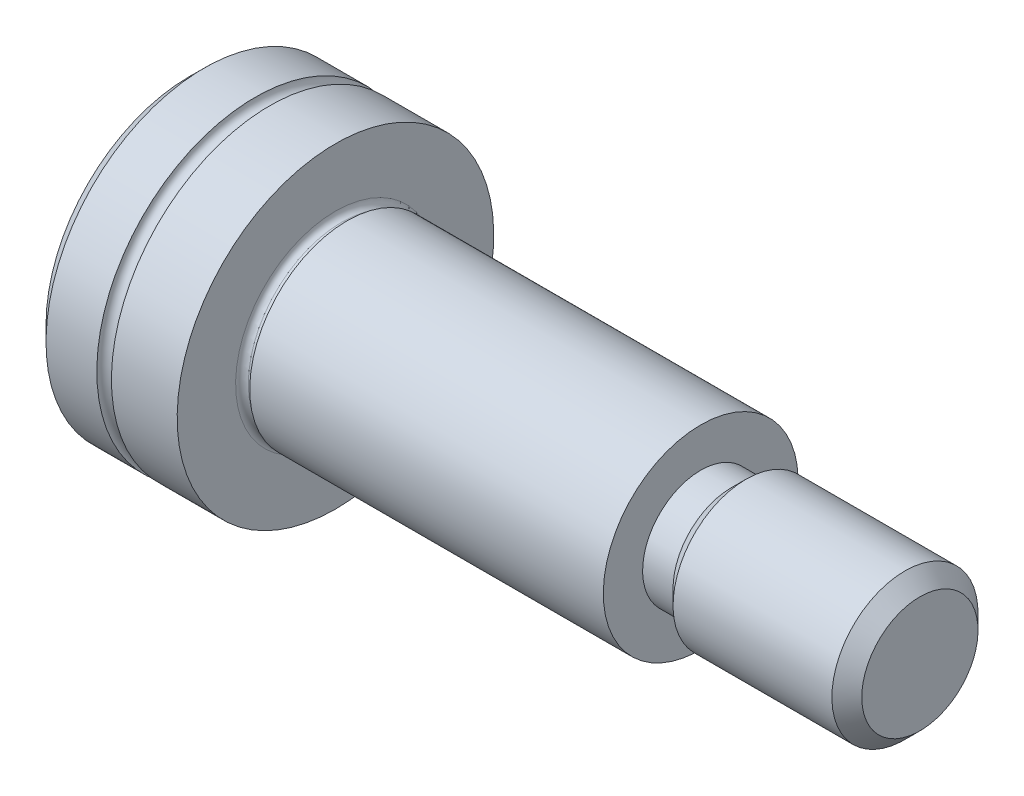
SolidWorks part; units mm, degrees
material "AISI 304"
ref_plane "Front Plane" through (0, 0, 0) normal (0, 0, 1) x (1, 0, 0)
ref_plane "Top Plane" through (0, 0, 0) normal (0, 1, 0) x (1, 0, 0)
ref_plane "Right Plane" through (0, 0, 0) normal (1, 0, 0) x (0, 0, -1)
ref_plane "Plane1" through (0, 0, 0) normal (0, 0, -1) x (-1, 0, 0)
sketch "Sketch1" plane through (0, 0, 0) normal (0, 0, -1) x (-1, 0, 0)
  line L0 (0, 6.5) -> (0, 0)
  line L1 (0, 0) -> (6, 0)
  line L2 (6, 0) -> (6, 6.5)
  line L3 (6, 6.5) -> (3.3, 6.5)
  line L4 (2.7, 6.5) -> (0, 6.5)
  line L5 (0, 0) -> (6, 0) construction
  arc A0 (3.3, 6.5) -> (2.7, 6.5) centre (3, 6.5) cw
revolve "Revolve1" add sketch "Sketch1" angle 360 about L5
sketch "Sketch2" plane through (0, 0, 0) normal (1, 0, 0) x (0, 0, -1)
  circle A0 centre (0, 0) radius 3.84
extrude "Boss-Extrude1" add sketch "Sketch2" along normal blind 0.3876
sketch "Sketch3" plane through (0.3876, 0, 0) normal (1, 0, 0) x (0, 0, -1)
  circle A0 centre (0, 0) radius 3.84
extrude "Boss-Extrude2" add sketch "Sketch3" along normal blind 0.0924 draft 60 draft outward yes
sketch "Sketch4" plane through (0.48, 0, 0) normal (1, 0, 0) x (0, 0, -1)
  circle A0 centre (0, 0) radius 4
extrude "Boss-Extrude3" add sketch "Sketch4" along normal blind 14.52
sketch "Sketch5" plane through (15, 0, 0) normal (1, 0, 0) x (0, 0, -1)
  circle A0 centre (0, 0) radius 2.3865
extrude "Boss-Extrude4" add sketch "Sketch5" along normal blind 1.25
sketch "Sketch6" plane through (16.25, 0, 0) normal (1, 0, 0) x (0, 0, -1)
  circle A0 centre (0, 0) radius 2.3865
extrude "Boss-Extrude5" add sketch "Sketch6" along normal blind 0.6135 draft 45 draft outward yes
sketch "Sketch7" plane through (16.8635, 0, 0) normal (1, 0, 0) x (0, 0, -1)
  circle A0 centre (0, 0) radius 3
extrude "Boss-Extrude6" add sketch "Sketch7" along normal blind 7.1365
sketch "Sketch8" plane through (-6, 0, 0) normal (-1, 0, 0) x (0, 0, 1)
  line L0 (2.5, -1.4434) -> (2.5, 1.4434)
  line L1 (2.5, 1.4434) -> (0, 2.8868)
  line L2 (0, 2.8868) -> (-2.5, 1.4434)
  line L3 (-2.5, 1.4434) -> (-2.5, -1.4434)
  line L4 (-2.5, -1.4434) -> (0, -2.8868)
  line L5 (0, -2.8868) -> (2.5, -1.4434)
extrude "Cut-Extrude1" cut sketch "Sketch8" against normal blind 3
sketch "Sketch9" plane through (0, 0, 0) normal (0, 0, 1) x (1, 0, 0)
  line L0 (-3, 2.4) -> (-3, 0)
  line L1 (-3, 0) -> (-1.6144, 0)
  line L2 (-1.6144, 0) -> (-3, 2.4)
  line L3 (-3, 0) -> (-1.6144, 0) construction
revolve "Cut-Revolve1" cut sketch "Sketch9" angle 360 about L3
chamfer "Chamfer1" distance 0.6135 angle 45 2 edges at (-6, -6.5, 0) (24, 3, 0)
fillet "Fillet1" radius 0.261 1 edges at (0, 3.84, 0)
